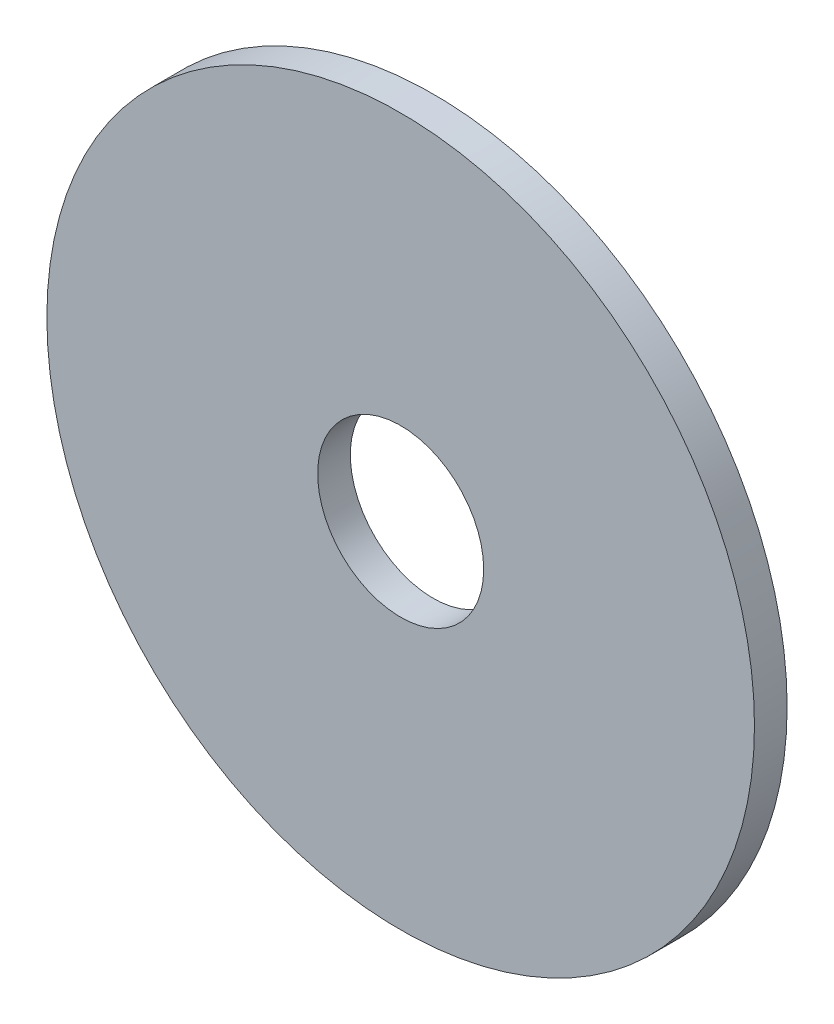
SolidWorks part; units mm, degrees
ref_plane "Front Plane" through (0, 0, 0) normal (0, 0, 1) x (1, 0, 0)
ref_plane "Top Plane" through (0, 0, 0) normal (0, 1, 0) x (1, 0, 0)
ref_plane "Right Plane" through (0, 0, 0) normal (1, 0, 0) x (0, 0, -1)
sketch "Sketch1" plane through (0, 0, 0) normal (0, 0, 1) x (1, 0, 0)
  circle A0 centre (0, 0) radius 65
  dimension "D1" = 130
extrude "Boss-Extrude1" add sketch "Sketch1" along normal blind 6
sketch "Sketch2" plane through (0, 0, 6) normal (0, 0, 1) x (1, 0, 0)
  circle A0 centre (0, 0) radius 15.25
  dimension "D1" = 30.5
extrude "Cut-Extrude1" cut sketch "Sketch2" against normal blind 6
